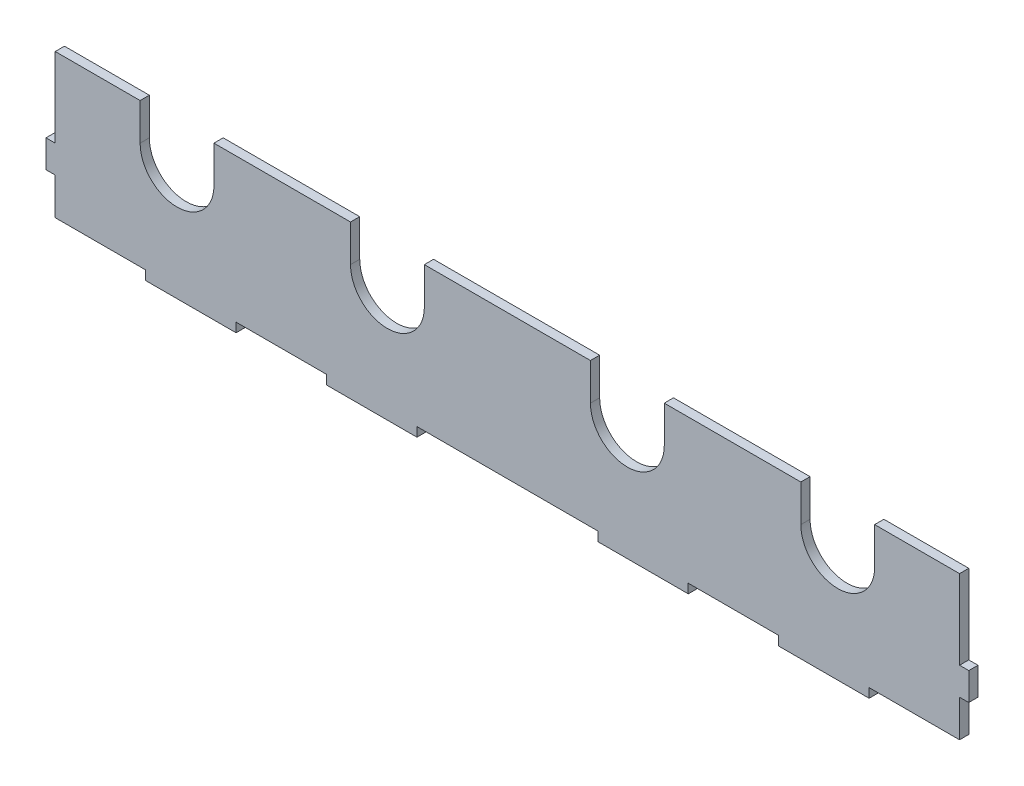
SolidWorks part; units mm, degrees
material "Contreplaqué pin"
ref_plane "Plan de face" through (0, 0, 0) normal (0, 0, 1) x (1, 0, 0)
ref_plane "Plan de dessus" through (0, 0, 0) normal (0, 1, 0) x (1, 0, 0)
ref_plane "Plan de droite" through (0, 0, 0) normal (1, 0, 0) x (0, 0, -1)
sketch "Esquisse1" plane through (0, 0, 0) normal (0, 0, 1) x (1, 0, 0)
  line L0 (0, 40) -> (0, 83)
  line L1 (49, 0) -> (98, 0)
  line L2 (0, 5) -> (0, 25)
  line L3 (0, 83) -> (46, 83)
  line L4 (490, 5) -> (490, 25)
  line L5 (0, 25) -> (-5, 25)
  line L7 (0, 40) -> (-5, 40)
  line L8 (-5, 25) -> (-5, 40)
  line L9 (490, 40) -> (490, 83)
  line L10 (490, 25) -> (495, 25)
  line L12 (490, 40) -> (495, 40)
  line L13 (495, 25) -> (495, 40)
  line L14 (0, 5) -> (49, 5)
  line L15 (49, 5) -> (49, 0)
  line L16 (49, 0) -> (98, 0)
  line L17 (98, 0) -> (98, 5)
  line L18 (98, 5) -> (147, 5)
  line L19 (147, 5) -> (147, 0)
  line L20 (147, 0) -> (196, 0)
  line L21 (196, 0) -> (196, 5)
  line L22 (196, 5) -> (245, 5)
  line L23 (245, 5) -> (294, 5)
  line L24 (294, 5) -> (294, 0)
  line L25 (294, 0) -> (343, 0)
  line L26 (343, 0) -> (343, 5)
  line L27 (343, 5) -> (392, 5)
  line L28 (392, 5) -> (392, 0)
  line L29 (392, 0) -> (441, 0)
  line L30 (441, 0) -> (441, 5)
  line L31 (441, 5) -> (490, 5)
  line L32 (392, 0) -> (441, 0)
  line L33 (294, 0) -> (343, 0)
  line L34 (147, 0) -> (196, 0)
  line L35 (86, 83) -> (160, 83)
  line L36 (200, 83) -> (290, 83)
  line L37 (330, 83) -> (404, 83)
  line L38 (444, 83) -> (490, 83)
  line L39 (46, 83) -> (46, 63)
  line L40 (86, 83) -> (86, 63)
  line L41 (160, 83) -> (160, 63)
  line L42 (200, 83) -> (200, 63)
  line L43 (290, 83) -> (290, 63)
  line L44 (330, 83) -> (330, 63)
  line L45 (404, 83) -> (404, 63)
  line L46 (444, 83) -> (444, 63)
  arc A4 (46, 63) -> (86, 63) centre (66, 63) ccw
  arc A5 (160, 63) -> (200, 63) centre (180, 63) ccw
  arc A6 (290, 63) -> (330, 63) centre (310, 63) ccw
  arc A7 (404, 63) -> (444, 63) centre (424, 63) ccw
  point P4 (416.5, 0)
  dimension "D18" = 40
  dimension "D20" = 20
  dimension "D15" = 20
  dimension "D23" = 20
  dimension "D4" = 15
  dimension "D5" = 5
  dimension "D7" = 15
  dimension "D8" = 5
  dimension "D1" = 500
  dimension "D9" = 49
  dimension "D6" = 25
  dimension "D2" = 49
  dimension "D3" = 5
  dimension "D10" = 83
  dimension "D11" = 25
  dimension "D13" = 66
  dimension "D19" = 40
  dimension "D12" = 20
  dimension "D14" = 114
  dimension "D21" = 20
  dimension "D17" = 20
  dimension "D24" = 20
  dimension "D16" = 114
  dimension "D22" = 66
extrude "Boss.-Extru.1" add sketch "Esquisse1" along normal blind 5 contours L30 L31 L4 L10 L13 L12 L9 L3 L0 L7 L8 L5 L2 L14 L15 L1 L17 L18 L19 L20 L21 L22 L23 L24 L25 L26 L27 L28 L29
equation "\"D12@Esquisse1\"=\"D18@Esquisse1\"/2"
equation "\"D21@Esquisse1\"=\"D20@Esquisse1\""
